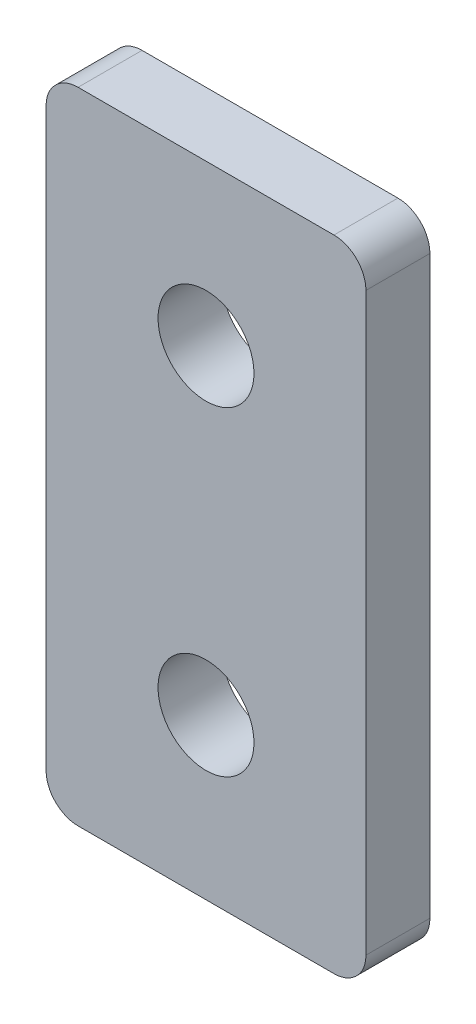
SolidWorks part; units mm, degrees
material "ABS"
ref_plane "前视基准面" through (0, 0, 0) normal (0, 0, 1) x (1, 0, 0)
ref_plane "上视基准面" through (0, 0, 0) normal (0, 1, 0) x (1, 0, 0)
ref_plane "右视基准面" through (0, 0, 0) normal (1, 0, 0) x (0, 0, -1)
other "Configuration Table"
sketch "草图1" plane through (0, 0, 0) normal (0, 0, 1) x (1, 0, 0)
  line L0 (1.6421, -1.909) -> (1.6421, -21.909) construction
  line L1 (-3.3579, -1.909) -> (6.6421, -1.909)
  line L2 (-3.3579, -1.909) -> (-3.3579, -21.909)
  line L3 (-3.3579, -21.909) -> (6.6421, -21.909)
  line L4 (6.6421, -1.909) -> (6.6421, -21.909)
  line L5 (-3.3579, -1.909) -> (6.6421, -21.909) construction
  line L6 (-3.3579, -21.909) -> (6.6421, -1.909) construction
  line L7 (-3.3579, -11.909) -> (6.6421, -11.909) construction
  circle A0 centre (1.6421, -6.909) radius 1.5
  circle A1 centre (1.6421, -11.909) radius 1.5 construction
  circle A2 centre (1.6421, -16.909) radius 1.5
  point P4 (1.6421, -11.909)
  dimension "D3" = 3
  dimension "D4" = 5
  dimension "D1" = 10
  dimension "D2" = 20
extrude "凸台-拉伸1" add sketch "草图1" along normal blind 2
fillet "圆角1" radius 1 4 edges at (-3.3579, -21.909, 1) (6.6421, -21.909, 1) (-3.3579, -1.909, 1) (6.6421, -1.909, 1)
